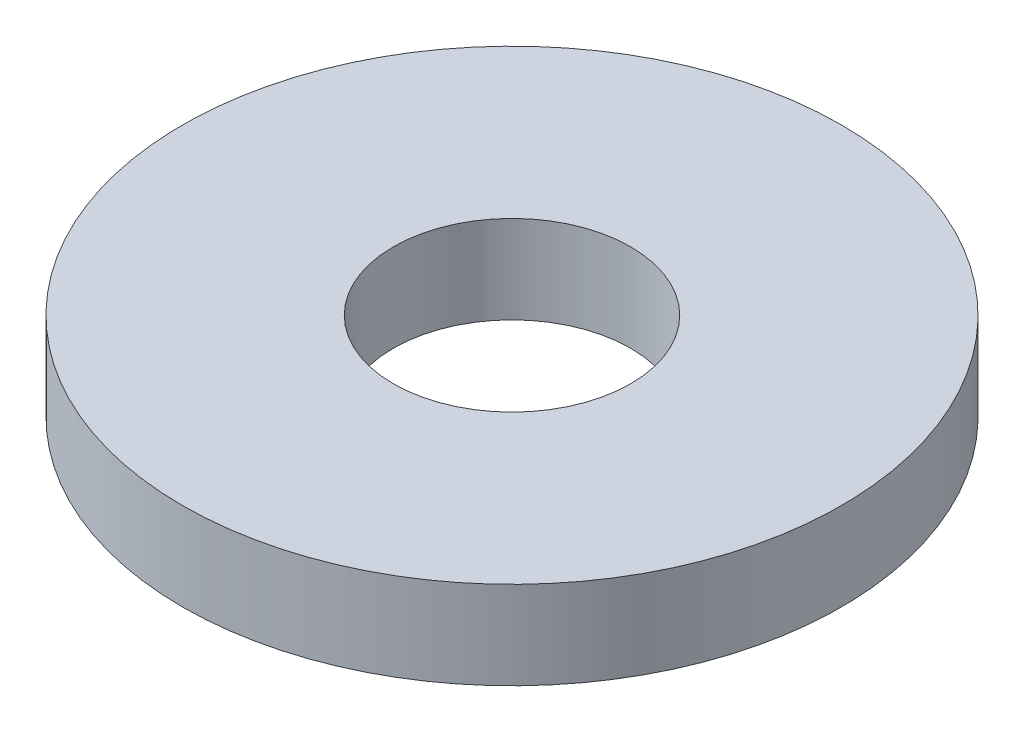
SolidWorks part; units mm, degrees
material "AISI 304"
ref_plane "Front Plane" through (0, 0, 0) normal (0, 0, 1) x (1, 0, 0)
ref_plane "Top Plane" through (0, 0, 0) normal (0, 1, 0) x (1, 0, 0)
ref_plane "Right Plane" through (0, 0, 0) normal (1, 0, 0) x (0, 0, -1)
sketch "Sketch1" plane through (0, 0, 0) normal (0, 1, 0) x (1, 0, 0)
  circle A0 centre (0, 0) radius 7.5
  circle A1 centre (0, 0) radius 2.7
  dimension "D1" = 5.4
  dimension "D2" = 15
extrude "Boss-Extrude1" add sketch "Sketch1" along normal blind 2
